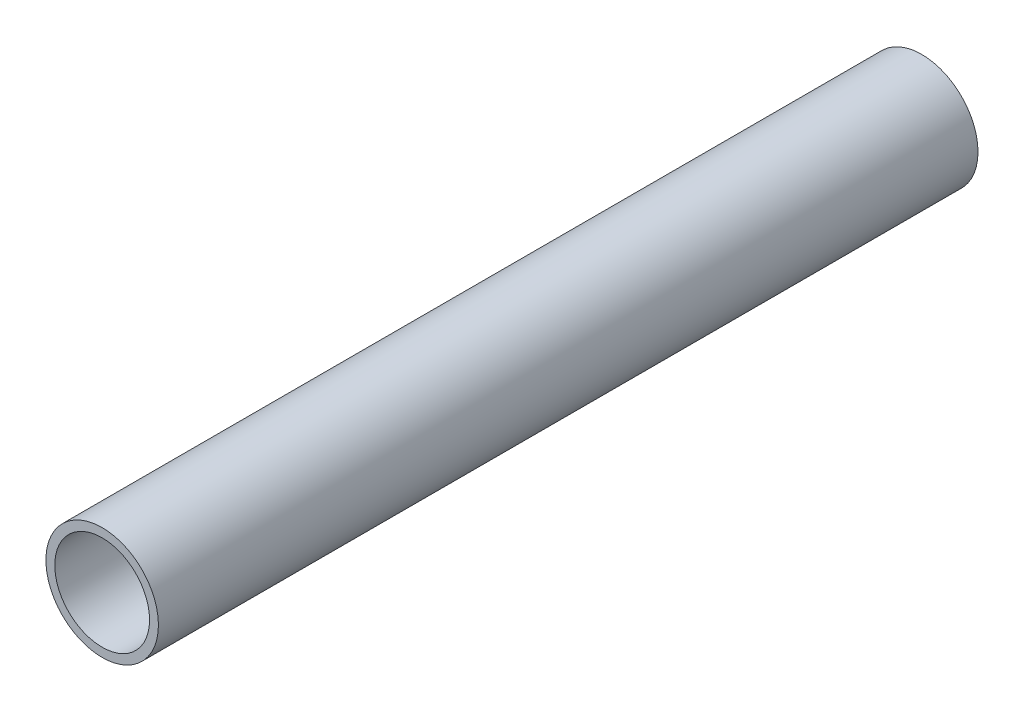
SolidWorks part; units mm, degrees
material "Hexcel AS4C (3000 Filaments)"
ref_plane "Front Plane" through (0, 0, 0) normal (0, 0, 1) x (1, 0, 0)
ref_plane "Top Plane" through (0, 0, 0) normal (0, 1, 0) x (1, 0, 0)
ref_plane "Right Plane" through (0, 0, 0) normal (1, 0, 0) x (0, 0, -1)
sketch "Sketch1" plane through (0, 0, 0) normal (0, 0, 1) x (1, 0, 0)
  circle A0 centre (0, 0) radius 12.7
  circle A1 centre (0, 0) radius 10.7
  dimension "D1" = 25.4
  dimension "D2" = 2
extrude "Boss-Extrude1" add sketch "Sketch1" along normal blind 185
